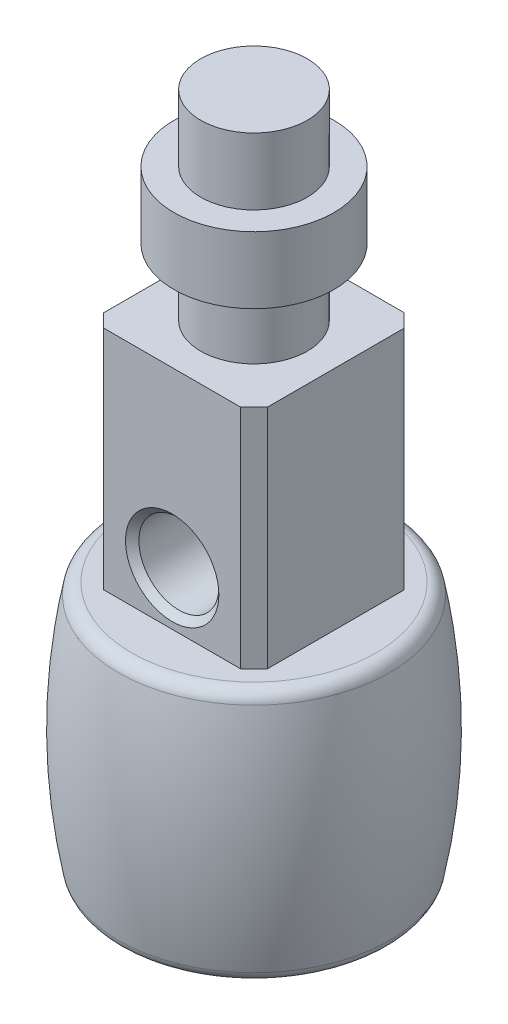
SolidWorks part; units mm, degrees
ref_plane "Front Plane" through (0, 0, 0) normal (0, 0, 1) x (1, 0, 0)
ref_plane "Top Plane" through (0, 0, 0) normal (0, 1, 0) x (1, 0, 0)
ref_plane "Right Plane" through (0, 0, 0) normal (1, 0, 0) x (0, 0, -1)
sketch "Sketch1" plane through (0, 0, 0) normal (0, 0, 1) x (1, 0, 0)
  line L0 (0, 0) -> (0, 51)
  line L1 (0, 51) -> (4, 51)
  line L2 (4, 51) -> (4, 46.0007)
  line L3 (4, 46.0007) -> (6, 46.0007)
  line L4 (6, 46.0007) -> (6, 40.9993)
  line L5 (6, 40.9993) -> (4, 40.9993)
  line L6 (4, 40.9993) -> (4, 36)
  line L7 (4, 36) -> (8, 36)
  line L8 (8, 36) -> (8, 19)
  line L9 (8, 19) -> (10, 19)
  line L10 (0, 0) -> (10, 0)
  arc A0 (10, 19) -> (10, 0) centre (-34.625, 9.5) cw
  point P14 (56.625, 9.5)
  point P15 (24.3421, 9.5)
  point P16 (20.7128, 9.5)
  point P17 (0, 0)
  point P18 (14.2035, 9.5)
  point P19 (11, 9.5)
  dimension "D1" = 36
  dimension "D2" = 19
  dimension "D3" = 15
  dimension "D4" = 4
  dimension "D5" = 6
  dimension "D6" = 8
  dimension "D7" = 11
  dimension "D8" = 5.0014
  dimension "D9" = 2
revolve "Revolve1" add sketch "Sketch1" angle 360 about L0
sketch "Sketch2" plane through (0, 36, 0) normal (0, 1, 0) x (1, 0, 0)
  line L0 (-6.1347, 5.1347) -> (-5.1347, 6.1347)
  line L1 (-5.1347, 6.1347) -> (5.1347, 6.1347)
  line L2 (-6.1347, 5.1347) -> (-6.1347, -5.1347)
  line L3 (-5.1347, -6.1347) -> (5.1347, -6.1347)
  line L4 (6.1347, 5.1347) -> (6.1347, -5.1347)
  line L5 (5.1347, 6.1347) -> (6.1347, 5.1347)
  line L6 (5.1347, -6.1347) -> (6.1347, -5.1347)
  line L7 (-6.1347, -5.1347) -> (-5.1347, -6.1347)
  circle A0 centre (0, 0) radius 8 construction
  circle A1 centre (0, 0) radius 8 construction
  point P0 (-6.1347, 6.1347)
  point P1 (6.1347, -6.1347)
  point P2 (-6.1347, -6.1347)
  point P3 (6.1347, 6.1347)
  point P4 (0, 0)
  point P5 (0, 0)
  point P8 (0, 0)
  point P9 (0, 0)
  point P10 (0, 0)
  point P11 (0, 0)
  point P18 (0, 0)
  point P21 (0, 0)
  point P22 (0, 0)
  point P23 (0, 0)
  point P24 (0, 0)
  point P27 (0, 0)
  point P28 (0, 0)
  point P29 (0, 0)
  point P30 (0, 0)
  point P31 (0, 0)
  point P32 (0, 0)
  point P33 (0, 0)
  point P34 (0, 0)
  point P35 (7.1318, -4.035)
  point P36 (0, 0)
  point P37 (7.6278, -2.4117)
  point P38 (5.5428, -5.7687)
  point P39 (6.1676, 5.0951)
  dimension "D1" = 1
  dimension "D2" = 1
extrude "Cut-Extrude1" cut sketch "Sketch2" against normal up to surface (17 mm away) flip side to cut up to face at (0, 19, -8)
sketch "Sketch3" plane through (0, 0, 6.1347) normal (0, 0, 1) x (1, 0, 0)
  line L0 (10, 19) -> (-10, 19) construction
  line L1 (-6.1347, 19) -> (-6.1347, 36) construction
  circle A0 centre (0.0003, 23) radius 3
  dimension "D1" = 6
  dimension "D2" = 4
  dimension "D3" = 6.135
extrude "Cut-Extrude2" cut sketch "Sketch3" against normal offset from surface (8.2694 mm away) 4 up to face at (0, 27.5, -6.1347)
chamfer "Chamfer1" distance 0.5 angle 45 1 edges at (3.0003, 23, 6.1347)
sketch "Sketch4" plane through (0, 0, 0) normal (0, -1, 0) x (1, 0, 0)
  circle A0 centre (0, 0) radius 5
  dimension "D1" = 10
extrude "Boss-Extrude1" add sketch "Sketch4" along normal blind 1
fillet "Fillet1" radius 1 2 edges at (0, 0, -10) (0, 19, -10)
